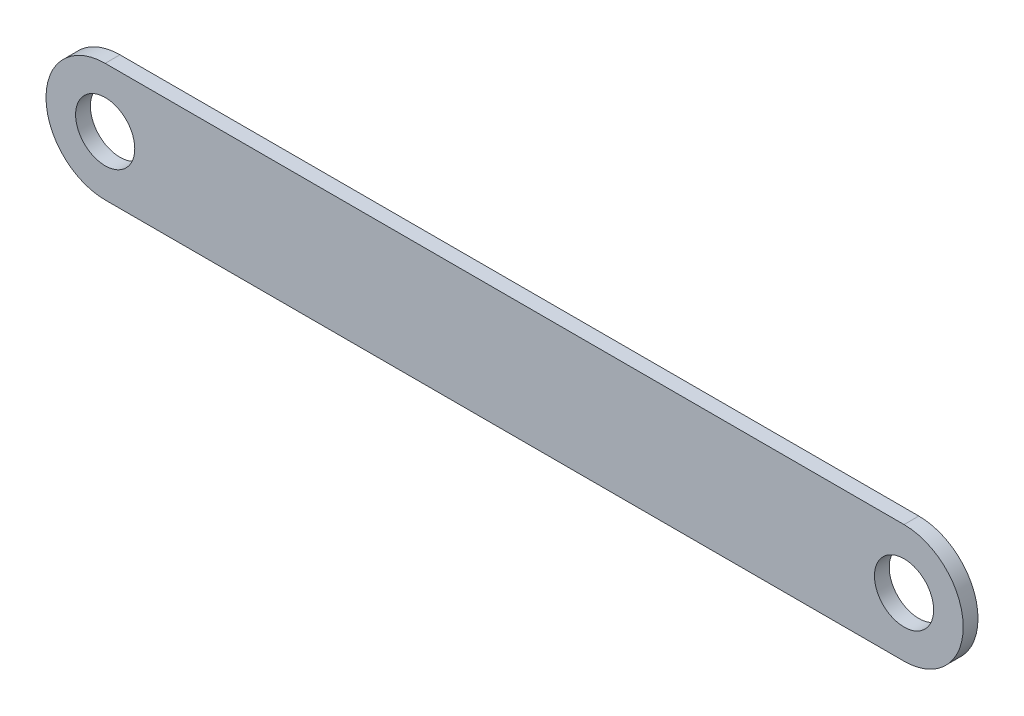
SolidWorks part; units mm, degrees
material "Pure Lead"
ref_plane "Front Plane" through (0, 0, 0) normal (0, 0, 1) x (1, 0, 0)
ref_plane "Top Plane" through (0, 0, 0) normal (0, 1, 0) x (1, 0, 0)
ref_plane "Right Plane" through (0, 0, 0) normal (1, 0, 0) x (0, 0, -1)
sketch "Sketch1" plane through (0, 0, 0) normal (0, 0, 1) x (1, 0, 0)
  line L0 (51.5131, 21.5571) -> (-218.4869, 21.5571)
  line L1 (-218.4869, -18.4429) -> (51.5131, -18.4429)
  arc A0 (51.5131, -18.4429) -> (51.5131, 21.5571) centre (51.5131, 1.5571) ccw
  arc A1 (-218.4869, 21.5571) -> (-218.4869, -18.4429) centre (-218.4869, 1.5571) ccw
  dimension "D2" = 20
  dimension "D1" = 270
extrude "Extrude1" add sketch "Sketch1" along normal blind 5
sketch "Sketch2" plane through (0, 0, 5) normal (0, 0, 1) x (1, 0, 0)
  circle A0 centre (-218.4869, 1.5571) radius 10
  circle A1 centre (51.5131, 1.5571) radius 10
  dimension "D1" = 20
extrude "Cut-Extrude1" cut sketch "Sketch2" against normal through all
